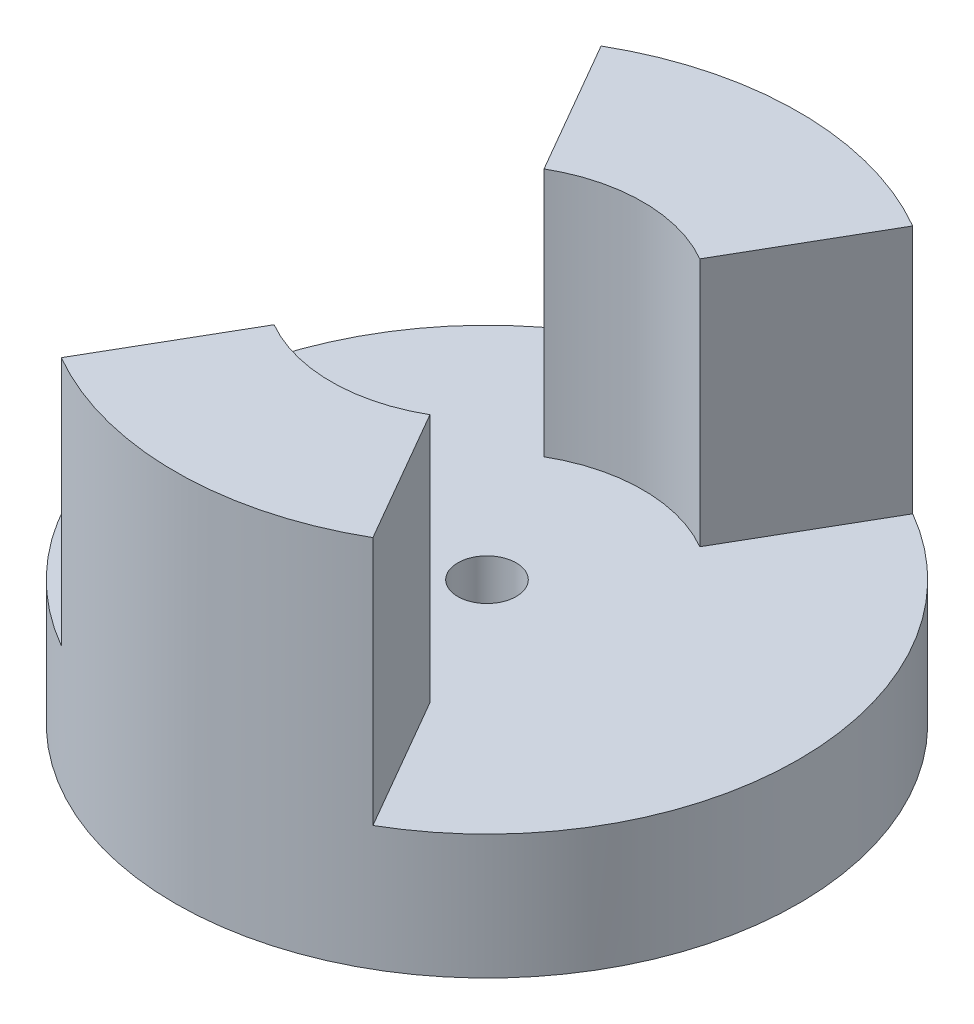
SolidWorks part; units mm, degrees
material "6061 Alloy"
ref_plane "Front Plane" through (0, 0, 0) normal (0, 0, 1) x (1, 0, 0)
ref_plane "Top Plane" through (0, 0, 0) normal (0, 1, 0) x (1, 0, 0)
ref_plane "Right Plane" through (0, 0, 0) normal (1, 0, 0) x (0, 0, -1)
sketch "Sketch1" plane through (0, 0, 0) normal (0, 1, 0) x (1, 0, 0)
  circle A0 centre (0, 0) radius 6.35
extrude "Boss-Extrude1" add sketch "Sketch1" along normal blind 7.62
hole_wizard "#0-80 Tapped Hole1" positions "Sketch2" profile "Sketch3" tap size "#0-80" standard "ANSI Inch" end condition through all
sketch "Sketch2" plane through (0, 7.62, 0) normal (0, 1, 0) x (1, 0, 0)
  point P0 (0, 0)
sketch "Sketch3" plane through (0, 7.62, 0) normal (1, 0, 0) x (0, 0, 1)
  line L0 (0, 0) -> (0, 7.62)
  line L1 (0, 7.62) -> (0.5956, 7.62)
  line L2 (0.5956, 7.62) -> (0.5956, 0)
  line L5 (0.5956, 0) -> (0, 0)
  line L11 (0, -6.35) -> (0, 107.95) construction
  dimension "Thru Tap Drill Dia." = 1.1913
  dimension "Thru Tap Drill Depth" = 7.62
cosmetic thread "Hole Thread1" parameters "D2"=1.524
sketch "Sketch4" plane through (0, 7.62, 0) normal (0, 1, 0) x (1, 0, 0)
  circle A0 centre (0, 0) radius 3.175
extrude "Cut-Extrude1" cut sketch "Sketch4" against normal blind 5.08
sketch "Sketch5" plane through (0, 7.62, 0) normal (0, 1, 0) x (1, 0, 0)
  line L0 (0, 0) -> (-7.62, -13.1982)
  line L1 (-7.62, -13.1982) -> (-7.62, 13.1982)
  line L2 (-7.62, 13.1982) -> (0, 0)
  line L3 (0, -4.191) -> (0, 4.191) construction
  point P4 (-6.9012, 7.3561)
  point P5 (-6.5716, 7.8385)
  dimension "D4" = 0
  dimension "D1" = 120
  dimension "D2" = 15.24
  dimension "D3" = 15.24
extrude "Cut-Extrude2" cut sketch "Sketch5" against normal blind 5.08
mirror "Mirror1" about plane through (0, 0, 0) normal (1, 0, 0) of "Cut-Extrude2"
